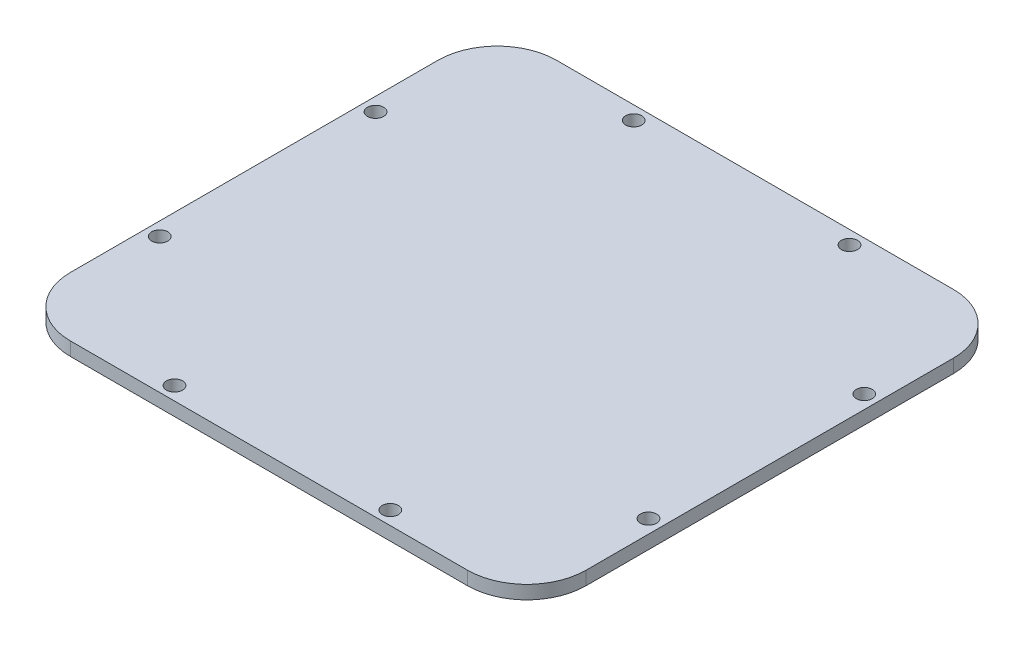
SolidWorks part; units mm, degrees
material "Delrin 2700 NC010, Low Viscosity Acetal Copolymer (SS)"
ref_plane "Front Plane" through (0, 0, 0) normal (0, 0, 1) x (1, 0, 0)
ref_plane "Top Plane" through (0, 0, 0) normal (0, 1, 0) x (1, 0, 0)
ref_plane "Right Plane" through (0, 0, 0) normal (1, 0, 0) x (0, 0, -1)
sketch "Sketch1" plane through (0, 0, 0) normal (0, 1, 0) x (1, 0, 0)
  line L1 (60.706, -57.2262) -> (-60.706, -57.2262)
  line L2 (60.706, -57.2262) -> (60.706, 57.2262)
  line L3 (60.706, 57.2262) -> (-60.706, 57.2262)
  line L4 (-60.706, -57.2262) -> (-60.706, 57.2262)
  line L5 (60.706, -57.2262) -> (-60.706, 57.2262) construction
  line L6 (60.706, 57.2262) -> (-60.706, -57.2262) construction
  point P0 (0, 0)
  dimension "D1" = 114.4524
  dimension "D2" = 121.412
extrude "Boss-Extrude1" add sketch "Sketch1" along normal blind 3.175
fillet "Fillet2" radius 13.97 4 edges at (60.706, 1.5875, -57.2262) (-60.706, 1.5875, 57.2262) (60.706, 1.5875, 57.2262) (-60.706, 1.5875, -57.2262)
hole_wizard "#6 Clearance Hole1" positions "Sketch2" profile "Sketch3" hole size "#6" standard "ANSI Inch" end condition through all
sketch "Sketch2" plane through (0, 0, 0) normal (0, 1, 0) x (1, 0, 0)
  line L28 (57.531, -43.2562) -> (57.531, 43.2562)
  line L29 (-46.736, -54.0512) -> (46.736, -54.0512)
  line L30 (-57.531, 43.2562) -> (-57.531, -43.2562)
  line L31 (46.736, 54.0512) -> (-46.736, 54.0512)
  line L32 (57.531, -43.2562) -> (57.531, 43.2562) construction
  line L33 (-46.736, -54.0512) -> (46.736, -54.0512) construction
  line L34 (-57.531, 43.2562) -> (-57.531, -43.2562) construction
  line L35 (46.736, 54.0512) -> (-46.736, 54.0512) construction
  arc A24 (57.531, 43.2562) -> (46.736, 54.0512) centre (46.736, 43.2562) ccw
  arc A25 (46.736, -54.0512) -> (57.531, -43.2562) centre (46.736, -43.2562) ccw
  arc A26 (-57.531, -43.2562) -> (-46.736, -54.0512) centre (-46.736, -43.2562) ccw
  arc A27 (-46.736, 54.0512) -> (-57.531, 43.2562) centre (-46.736, 43.2562) ccw
  arc A28 (57.531, 43.2562) -> (46.736, 54.0512) centre (46.736, 43.2562) ccw construction
  arc A29 (46.736, -54.0512) -> (57.531, -43.2562) centre (46.736, -43.2562) ccw construction
  arc A30 (-57.531, -43.2562) -> (-46.736, -54.0512) centre (-46.736, -43.2562) ccw construction
  arc A31 (-46.736, 54.0512) -> (-57.531, 43.2562) centre (-46.736, 43.2562) ccw construction
  point P141 (-25.4, 54.0512)
  point P143 (-57.531, 25.4)
  point P145 (-57.531, -25.4)
  point P147 (-25.4, -54.0512)
  dimension "D2" = 25.4
  dimension "D3" = 25.4
  dimension "D4" = 25.4
  dimension "D1" = 3.175
sketch "Sketch3" plane through (-25.4, 0, 54.0512) normal (1, 0, 0) x (0, 0, -1)
  line L0 (0, 0) -> (0, 3.175)
  line L1 (0, 3.175) -> (1.8986, 3.175)
  line L2 (1.8986, 3.175) -> (1.8986, 0)
  line L5 (1.8986, 0) -> (0, 0)
  line L11 (0, -6.35) -> (0, 107.95) construction
  dimension "Thru Hole Dia." = 3.7973
  dimension "Thru Hole Depth" = 3.175
mirror "Mirror1" about plane through (0, 0, 0) normal (1, 0, 0) of "#6 Clearance Hole1"
equation "\"D3@Sketch2\"=\"D2@Sketch2\""
equation "\"D4@Sketch2\"=\"D3@Sketch2\""
